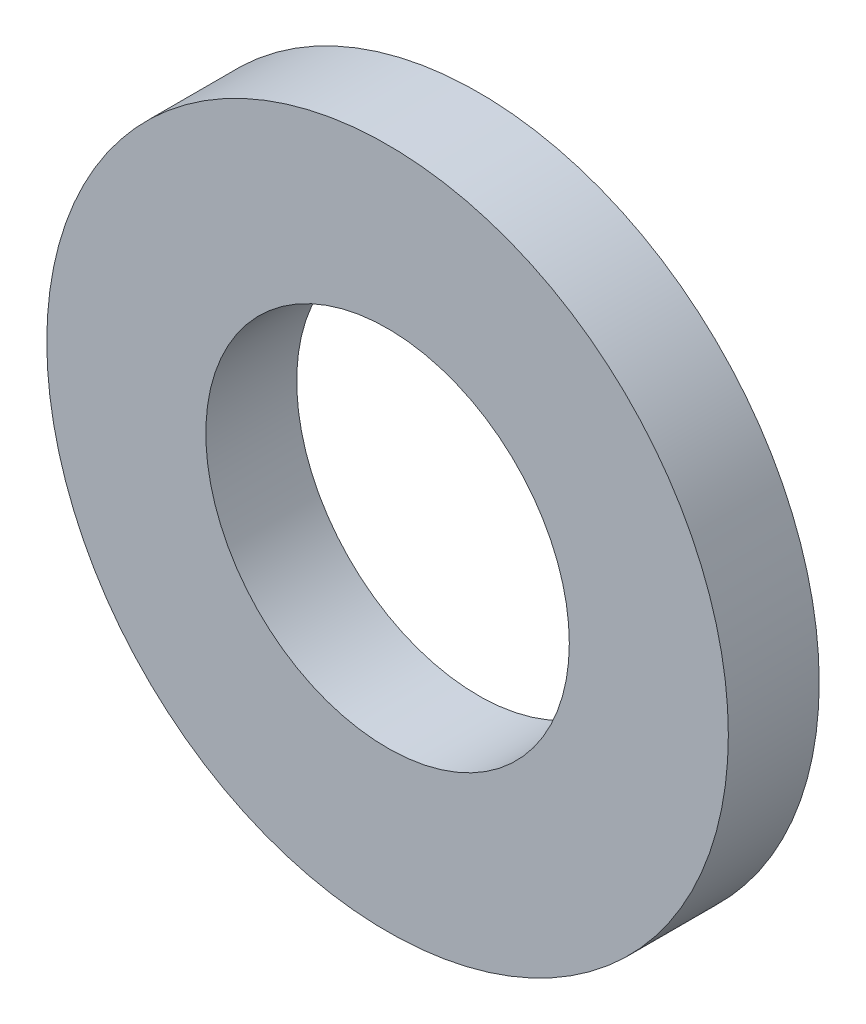
SolidWorks part; units mm, degrees
ref_plane "Front" through (0, 0, 0) normal (0, 0, 1) x (1, 0, 0)
ref_plane "Top" through (0, 0, 0) normal (0, 1, 0) x (1, 0, 0)
ref_plane "Right" through (0, 0, 0) normal (1, 0, 0) x (0, 0, -1)
sketch "Sketch1" plane through (0, 0, 0) normal (0, 0, 1) x (1, 0, 0)
  circle A0 centre (0, 0) radius 3.2
  circle A1 centre (0, 0) radius 6
  dimension "d1" = 6.4
  dimension "d2" = 12
extrude "Base-Extrude" add sketch "Sketch1" against normal blind 1.6
